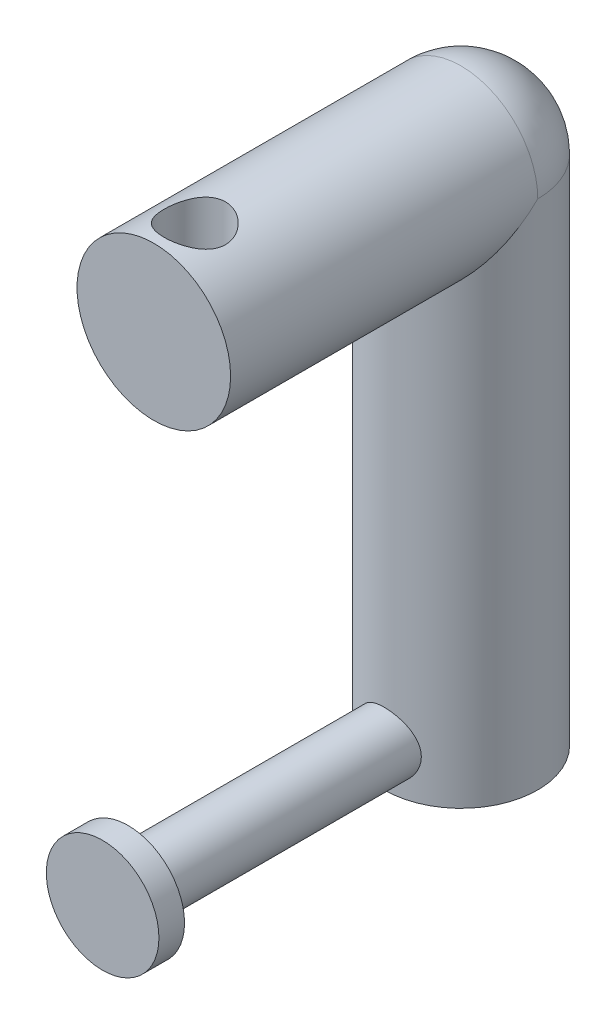
SolidWorks part; units mm, degrees
ref_plane "Front Plane" through (0, 0, 0) normal (0, 0, 1) x (1, 0, 0)
ref_plane "Top Plane" through (0, 0, 0) normal (0, 1, 0) x (1, 0, 0)
ref_plane "Right Plane" through (0, 0, 0) normal (1, 0, 0) x (0, 0, -1)
sketch "Sketch1" plane through (0, 0, 0) normal (0, 1, 0) x (1, 0, 0)
  circle A0 centre (0, 0) radius 15
  dimension "D1" = 30
extrude "Boss-Extrude1" add sketch "Sketch1" along normal blind 100
ref_plane "Plane1" through (0, 0, 15) normal (0, 0, 1) x (1, 0, 0)
sketch "Sketch2" plane through (0, 0, 15) normal (0, 0, 1) x (1, 0, 0)
  circle A0 centre (0, 8) radius 6
  dimension "D1" = 12
  dimension "D2" = 8
extrude "Boss-Extrude2" add sketch "Sketch2" along normal blind 50 and the other way up to surface separate body other way up to face at (0, 100, 15)
sketch "Sketch3" plane through (0, 0, 0) normal (0, 0, 1) x (1, 0, 0)
  line L0 (0, 100) -> (0, 115)
  line L1 (15, 100) -> (-15, 100) construction
  line L2 (-15, 100) -> (-15, 0) construction
  line L3 (-15, 100) -> (0, 100)
  arc A0 (0, 115) -> (-15, 100) centre (0, 100) ccw
revolve "Revolve1" add sketch "Sketch3" angle 180 about L0
sketch "Sketch4" plane through (0, 0, 0) normal (0, 0, 1) x (1, 0, 0)
  line L1 (-15, 100) -> (15, 100)
  arc A1 (15, 100) -> (-15, 100) centre (0, 100) ccw
  circle A2 centre (0, 100) radius 15
  dimension "D1" = 0
extrude "Boss-Extrude3" add sketch "Sketch4" along normal blind 60
ref_plane "Plane2" through (0, 115, 0) normal (0, 1, 0) x (1, 0, 0)
sketch "Sketch5" plane through (0, 115, 0) normal (0, 1, 0) x (1, 0, 0)
  line L0 (-15, -60) -> (15, -60) construction
  circle A0 centre (0, -52) radius 6
  dimension "D1" = 12
  dimension "D2" = 8
extrude "Cut-Extrude1" cut sketch "Sketch5" against normal up to next (30 mm away) contours A0
sketch "Sketch6" plane through (0, 0, 65) normal (0, 0, 1) x (1, 0, 0)
  circle A0 centre (0, 8) radius 11
  dimension "D1" = 22
extrude "Boss-Extrude4" add sketch "Sketch6" along normal blind 5
